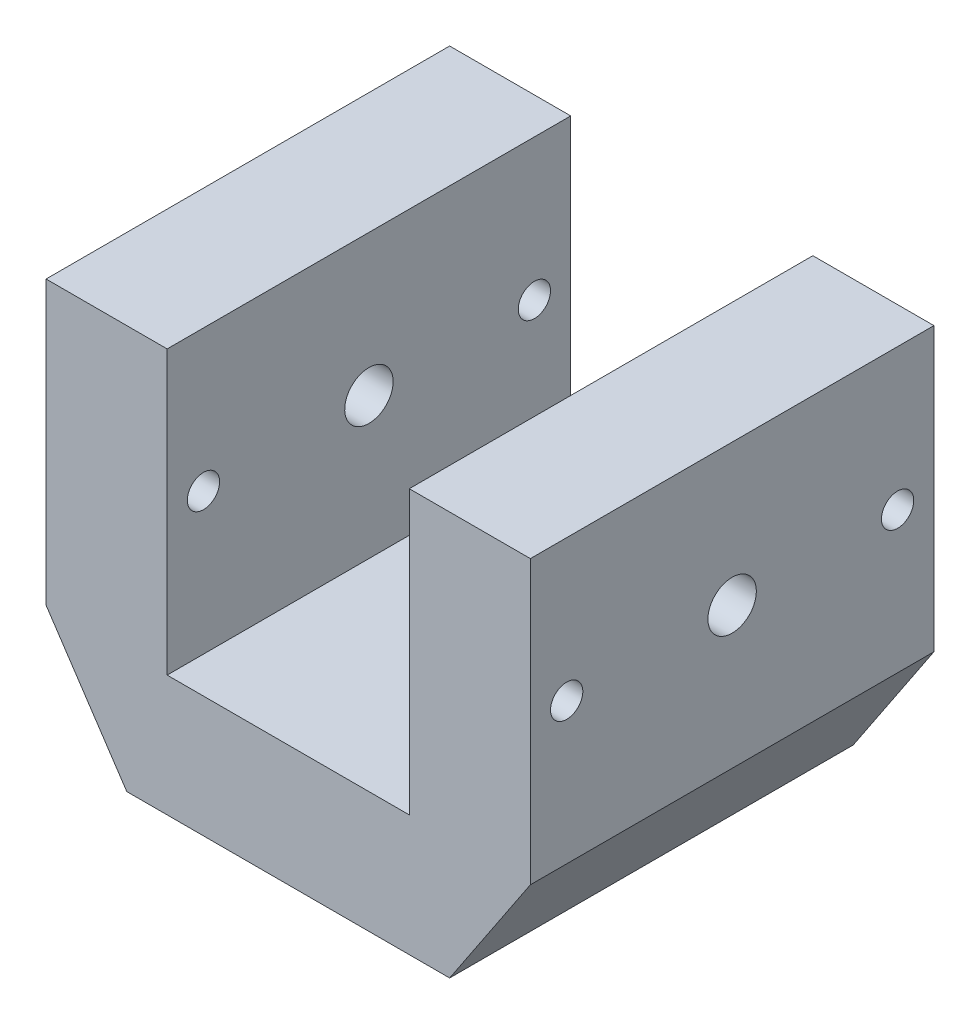
SolidWorks part; units mm, degrees
ref_plane "Płaszczyzna przednia" through (0, 0, 0) normal (0, 0, 1) x (1, 0, 0)
ref_plane "Płaszczyzna górna" through (0, 0, 0) normal (0, 1, 0) x (1, 0, 0)
ref_plane "Płaszczyzna prawa" through (0, 0, 0) normal (1, 0, 0) x (0, 0, -1)
sketch "Sketch1" plane through (0, 0, 0) normal (0, 0, 1) x (1, 0, 0)
  line L0 (-60, -50) -> (-60, 50)
  line L5 (-60, -50) -> (60, -50)
  line L7 (-60, 50) -> (60, 50)
  line L8 (60, -50) -> (60, 50)
  line L9 (-60, -50) -> (60, 50) construction
  line L10 (-60, 50) -> (60, -50) construction
  point P1 (0, 0)
  dimension "D1" = 100
  dimension "D2" = 120
extrude "Boss-Extrude1" add sketch "Sketch1" along normal blind 100
sketch "Sketch2" plane through (0, 0, 0) normal (0, 0, 1) x (1, 0, 0)
  line L24 (0, 50) -> (0, -50) construction
  line L25 (-60, -50) -> (60, -50) construction
  line L26 (-60, -20) -> (-40, -50)
  line L27 (-60, 50) -> (-60, -50) construction
  line L28 (30, 50) -> (30, -20)
  line L29 (-60, -20) -> (-60, -50)
  line L30 (-60, -50) -> (-40, -50)
  line L31 (-30, 50) -> (-30, -20)
  line L32 (60, 50) -> (-60, 50) construction
  line L33 (-30, -20) -> (30, -20)
  line L34 (-30, 50) -> (30, 50)
  line L35 (60, -50) -> (40, -50)
  line L36 (60, -20) -> (60, -50)
  line L37 (60, -20) -> (40, -50)
  point P18 (0, 0)
  dimension "D1" = 20
  dimension "D2" = 30
  dimension "D3" = 30
extrude "Cut-Extrude2" cut sketch "Sketch2" along normal through all both and the other way through all
sketch "Sketch3" plane through (0, 0, 0) normal (0, 1, 0) x (1, 0, 0)
  line L0 (-60, -50) -> (60, -50) construction
  line L1 (-60, -100) -> (-60, 0) construction
  line L2 (60, -100) -> (60, 0) construction
  line L3 (0, 0) -> (0, -100) construction
  line L4 (30, 0) -> (-30, 0) construction
  line L5 (-30, -100) -> (30, -100) construction
  circle A1 centre (0, -50) radius 6
  dimension "D3" = 12
extrude "Cut-Extrude3" cut sketch "Sketch3" against normal through all both
sketch "Sketch5" plane through (0, 0, 0) normal (1, 0, 0) x (0, 0, -1)
  line L0 (-100, 15) -> (0, 15) construction
  line L1 (-100, -20) -> (-100, 50) construction
  line L2 (0, -20) -> (0, 50) construction
  circle A0 centre (-91, 15) radius 4
  circle A1 centre (-9, 15) radius 4
  dimension "D1" = 8
  dimension "D2" = 9
  dimension "D3" = 9
extrude "Cut-Extrude4" cut sketch "Sketch5" against normal through all both and the other way through all
sketch "Sketch6" plane through (0, 0, 0) normal (1, 0, 0) x (0, 0, -1)
  line L0 (-100, 15) -> (0, 15) construction
  line L1 (-100, -20) -> (-100, 50) construction
  line L2 (0, -20) -> (0, 50) construction
  line L3 (-50, 50) -> (-50, -20) construction
  line L4 (-100, 50) -> (0, 50) construction
  line L5 (-100, -20) -> (0, -20) construction
  circle A0 centre (-50, 15) radius 6
  dimension "D1" = 12
extrude "Cut-Extrude5" cut sketch "Sketch6" against normal through all and the other way through all
sketch "Sketch7" plane through (0, 0, 0) normal (0, 1, 0) x (1, 0, 0)
  circle A0 centre (0, -50) radius 11
  dimension "D1" = 22
extrude "Cut-Extrude7" cut sketch "Sketch7" against normal blind 13 from surface at -20 starting at face at (-6, -20, 50)
